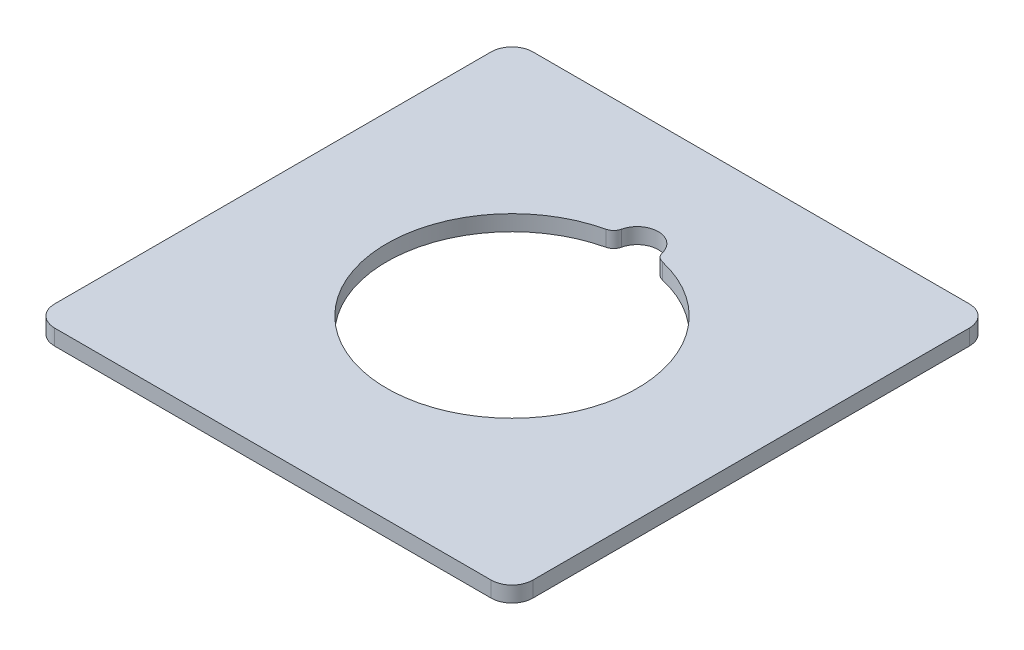
SolidWorks part; units mm, degrees
material "Poliüretan Köpük Esnek"
ref_plane "Ön Düzlem" through (0, 0, 0) normal (0, 0, 1) x (1, 0, 0)
ref_plane "Üst Düzlem" through (0, 0, 0) normal (0, 1, 0) x (1, 0, 0)
ref_plane "Sağ Düzlem" through (0, 0, 0) normal (1, 0, 0) x (0, 0, -1)
sketch "Çizim1" plane through (0, 0, 0) normal (0, 1, 0) x (1, 0, 0)
  line L1 (-20.9, -22.9) -> (20.9, -22.9)
  line L2 (-22.9, -20.9) -> (-22.9, 20.9)
  line L3 (-20.9, 22.9) -> (20.9, 22.9)
  line L4 (22.9, -20.9) -> (22.9, 20.9)
  line L5 (-22.9, -22.9) -> (22.9, 22.9) construction
  line L6 (-22.9, 22.9) -> (22.9, -22.9) construction
  arc A0 (20.9, -22.9) -> (22.9, -20.9) centre (20.9, -20.9) ccw
  arc A1 (-20.9, -22.9) -> (-22.9, -20.9) centre (-20.9, -20.9) cw
  arc A2 (20.9, 22.9) -> (22.9, 20.9) centre (20.9, 20.9) cw
  arc A3 (-22.9, 20.9) -> (-20.9, 22.9) centre (-20.9, 20.9) cw
  arc A4 (-2.705, 11.6911) -> (2.705, 11.6911) centre (0, 0) ccw
  arc A5 (-1.9557, 12.4419) -> (1.9557, 12.4419) centre (0, 11.9935) cw
  arc A6 (1.9557, 12.4419) -> (2.705, 11.6911) centre (2.9305, 12.6654) ccw
  arc A7 (-1.9557, 12.4419) -> (-2.705, 11.6911) centre (-2.9305, 12.6654) cw
  point P0 (0, 0)
  dimension "D2" = 2
  dimension "D3" = 24
  dimension "D4" = 1
  dimension "D1" = 45.8
extrude "Yükseklik-Ekstrüzyon1" add sketch "Çizim1" along normal blind 1.5
